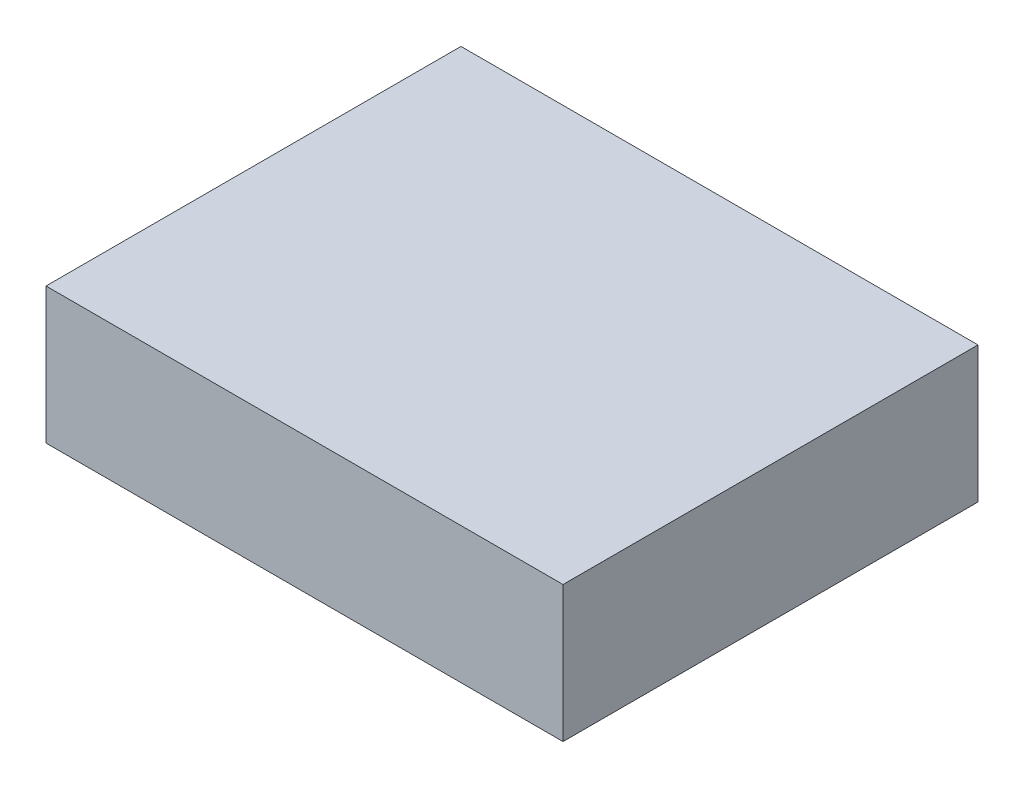
SolidWorks part; units mm, degrees
ref_plane "Front Plane" through (0, 0, 0) normal (0, 0, 1) x (1, 0, 0)
ref_plane "Top Plane" through (0, 0, 0) normal (0, 1, 0) x (1, 0, 0)
ref_plane "Right Plane" through (0, 0, 0) normal (1, 0, 0) x (0, 0, -1)
sketch "Sketch1" plane through (0, 0, 0) normal (0, 1, 0) x (1, 0, 0)
  line L1 (-28.7292, 15.2306) -> (47.2708, 15.2306)
  line L2 (-28.7292, 15.2306) -> (-28.7292, -45.7694)
  line L3 (-28.7292, -45.7694) -> (47.2708, -45.7694)
  line L4 (47.2708, 15.2306) -> (47.2708, -45.7694)
  dimension "D1" = 76
  dimension "D2" = 61
extrude "Boss-Extrude1" add sketch "Sketch1" along normal blind 20
